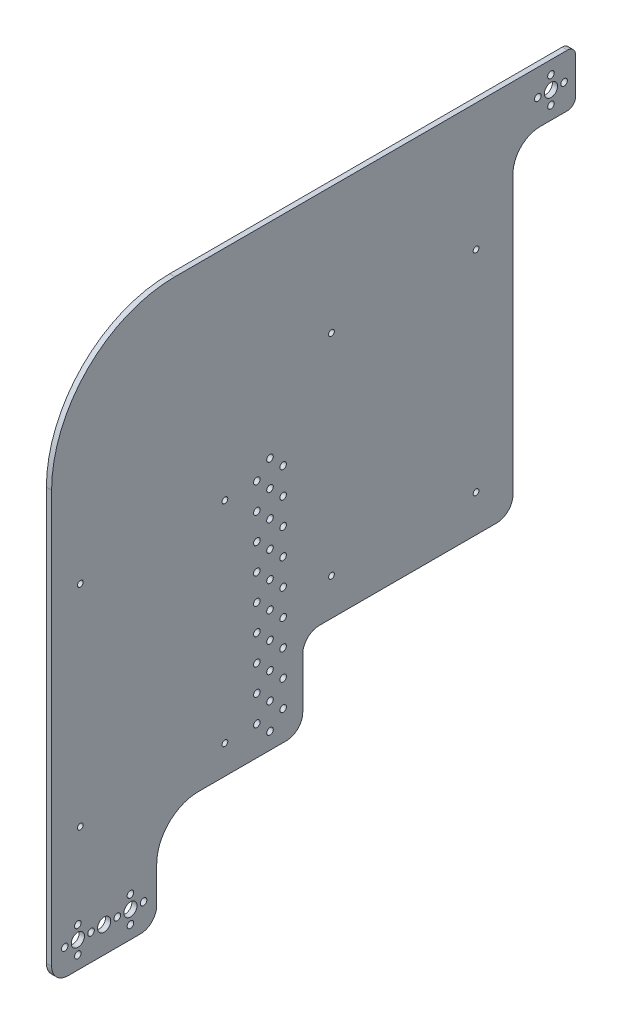
SolidWorks part; units mm, degrees
ref_plane "Front" through (0, 0, 0) normal (0, 0, 1) x (1, 0, 0)
ref_plane "Top" through (0, 0, 0) normal (0, 1, 0) x (1, 0, 0)
ref_plane "Right" through (0, 0, 0) normal (1, 0, 0) x (0, 0, -1)
sketch "Sketch1" plane through (0, 0, 0) normal (1, 0, 0) x (0, 0, -1)
  line L0 (-248, -304) -> (-264, -304) construction
  line L1 (-272, -300) -> (-272, -308) construction
  line L2 (-240, -288) -> (-240, -310)
  line L3 (-250, -320) -> (-294, -320)
  line L4 (-304, -310) -> (-304, -288)
  line L5 (-16, 16) -> (10, 16)
  line L6 (15, 11) -> (15, -11)
  line L7 (10, -16) -> (-6.55, -16)
  line L8 (-240, -288) -> (-6.55, -16) construction
  line L9 (-229, 16) -> (-16, 16)
  line L10 (-304, -288) -> (-304, -59)
  line L11 (-151.1, -252.6) -> (-151.1, -221.8)
  line L12 (-141.1, -211.8) -> (-33.1, -211.8)
  line L13 (-23.1, -201.8) -> (-23.1, -32.55)
  line L14 (-214.6, -262.6) -> (-161.1, -262.6)
  line L15 (-6.55, -16) -> (-23.1, -16) construction
  line L16 (-191, -252.6) -> (-151.1, -252.6) construction
  line L17 (-179.05, -244.6) -> (-179.05, -228.6) construction
  line L18 (-286.5, -117.1) -> (-286.5, -245.1) construction
  line L19 (-294, -109.6) -> (-191, -109.6) construction
  line L20 (-294, -109.6) -> (-294, -252.6) construction
  line L21 (-294, -252.6) -> (-191, -252.6) construction
  line L22 (-191, -109.6) -> (-191, -252.6) construction
  line L23 (-286.5, -245.1) -> (-198.5, -245.1) construction
  line L24 (-198.5, -117.1) -> (-198.5, -245.1) construction
  line L25 (-286.5, -117.1) -> (-198.5, -117.1) construction
  line L26 (-133.6, -61.3) -> (-133.6, -189.3) construction
  line L27 (-141.1, -53.8) -> (-38.1, -53.8) construction
  line L28 (-141.1, -53.8) -> (-141.1, -196.8) construction
  line L29 (-141.1, -196.8) -> (-38.1, -196.8) construction
  line L30 (-38.1, -53.8) -> (-38.1, -196.8) construction
  line L31 (-133.6, -189.3) -> (-45.6, -189.3) construction
  line L32 (-45.6, -61.3) -> (-45.6, -189.3) construction
  line L33 (-133.6, -61.3) -> (-45.6, -61.3) construction
  circle A0 centre (-256, -304) radius 4
  circle A1 centre (0, 0) radius 4
  circle A2 centre (8, 0) radius 2
  circle A3 centre (0, -8) radius 2
  circle A4 centre (-8, 0) radius 2
  circle A5 centre (0, 8) radius 2
  circle A6 centre (-248, -304) radius 2
  circle A7 centre (-256, -312) radius 2
  circle A8 centre (-264, -304) radius 2 [skipped]
  circle A9 centre (-256, -296) radius 2
  circle A10 centre (-264, -304) radius 2
  circle A11 centre (-272, -304) radius 4
  circle A12 centre (-288, -312) radius 2
  circle A13 centre (-280, -304) radius 2
  circle A14 centre (-288, -296) radius 2
  circle A15 centre (-288, -304) radius 4
  circle A16 centre (-296, -304) radius 2
  arc A17 (-240, -310) -> (-250, -320) centre (-250, -310) cw
  arc A18 (-294, -320) -> (-304, -310) centre (-294, -310) cw
  arc A19 (10, 16) -> (15, 11) centre (10, 11) cw
  arc A20 (15, -11) -> (10, -16) centre (10, -11) cw
  arc A21 (-304, -59) -> (-229, 16) centre (-229, -59) cw
  arc A22 (-240, -288) -> (-214.6, -262.6) centre (-214.6, -288) cw
  arc A23 (-6.55, -16) -> (-23.1, -32.55) centre (-6.55, -32.55) ccw
  arc A24 (-33.1, -211.8) -> (-23.1, -201.8) centre (-33.1, -201.8) ccw
  arc A25 (-151.1, -252.6) -> (-161.1, -262.6) centre (-161.1, -252.6) cw
  arc A26 (-151.1, -221.8) -> (-141.1, -211.8) centre (-141.1, -221.8) cw
  circle A27 centre (-171.05, -252.6) radius 2
  circle A28 centre (-179.05, -244.6) radius 2
  circle A29 centre (-171.05, -236.6) radius 2
  circle A30 centre (-163.05, -244.6) radius 2
  circle A31 centre (-179.05, -228.6) radius 2
  circle A32 centre (-171.05, -220.6) radius 2
  circle A33 centre (-163.05, -228.6) radius 2
  circle A34 centre (-179.05, -212.6) radius 2
  circle A35 centre (-171.05, -204.6) radius 2
  circle A36 centre (-163.05, -212.6) radius 2
  circle A37 centre (-179.05, -196.6) radius 2
  circle A38 centre (-171.05, -188.6) radius 2
  circle A39 centre (-163.05, -196.6) radius 2
  circle A40 centre (-179.05, -180.6) radius 2
  circle A41 centre (-171.05, -172.6) radius 2
  circle A42 centre (-163.05, -180.6) radius 2
  circle A43 centre (-179.05, -164.6) radius 2
  circle A44 centre (-171.05, -156.6) radius 2
  circle A45 centre (-163.05, -164.6) radius 2
  circle A46 centre (-179.05, -148.6) radius 2
  circle A47 centre (-171.05, -140.6) radius 2
  circle A48 centre (-163.05, -148.6) radius 2
  circle A49 centre (-179.05, -132.6) radius 2
  circle A50 centre (-171.05, -124.6) radius 2
  circle A51 centre (-163.05, -132.6) radius 2
  circle A52 centre (-179.05, -116.6) radius 2
  circle A53 centre (-171.05, -108.6) radius 2
  circle A54 centre (-163.05, -116.6) radius 2
  circle A55 centre (-286.5, -117.1) radius 1.75
  circle A56 centre (-198.5, -117.1) radius 1.75
  circle A57 centre (-198.5, -245.1) radius 1.75
  circle A58 centre (-286.5, -245.1) radius 1.75
  circle A59 centre (-133.6, -61.3) radius 1.75
  circle A60 centre (-45.6, -61.3) radius 1.75
  circle A61 centre (-45.6, -189.3) radius 1.75
  circle A62 centre (-133.6, -189.3) radius 1.75
  point P18 (0, 0)
  point P27 (-256, -304)
  point P47 (-272, -320)
  point P58 (15, 0)
  point P75 (-151.1, -262.6)
  point P78 (-151.1, -211.8)
  point P81 (0, 0)
  point P91 (-171.05, -244.6)
  dimension "D1" = 8
  dimension "D4" = 4
  dimension "D14" = 10
  dimension "D15" = 5
  dimension "D19" = 75
  dimension "D24" = 10
  dimension "D27" = 3.5
  dimension "D40" = 3.5
  dimension "D2" = 256
  dimension "D3" = 304
  dimension "D5" = 8
  dimension "D7" = 8
  dimension "D10" = 16
  dimension "D11" = 16
  dimension "D12" = 16
  dimension "D13" = 16
  dimension "D16" = 15
  dimension "D17" = 16
  dimension "D18" = 16
  dimension "D20" = 88.9
  dimension "D21" = 25.4
  dimension "D22" = 50.8
  dimension "D23" = 38.1
  dimension "D25" = 10
  dimension "D26" = 10
  dimension "D28" = 143
  dimension "D29" = 4
  dimension "D30" = 8
  dimension "D32" = 16
  dimension "D33" = 103
  dimension "D34" = 7.5
  dimension "D35" = 7.5
  dimension "D36" = 7.5
  dimension "D37" = 7.5
  dimension "D38" = 15
  dimension "D39" = 15
  dimension "D41" = 143
  dimension "D42" = 103
  dimension "D43" = 7.5
  dimension "D44" = 7.5
  dimension "D45" = 7.5
  dimension "D46" = 7.5
  dimension "D9" = 2
  dimension "D31" = 9
  dimension "D6" = 4
  dimension "D8" = 4
extrude "Boss-Extrude1" add sketch "Sketch1" against normal blind 3.175
sketch "Sketch2" plane through (0, 0, 0) normal (1, 0, 0) x (0, 0, -1)
  line L0 (-252.45, -60.2) -> (-74.65, -60.2) construction
  line L1 (-304, -60.2) -> (-252.45, -60.2) construction
  line L2 (-304, -59) -> (-304, -310) construction
  line L3 (-74.65, -60.2) -> (-23.1, -60.2) construction
  line L4 (-23.1, -201.8) -> (-23.1, -32.55) construction
  line L5 (10, 16) -> (-229, 16) construction
  text T0 "8699" font "Century Gothic" height 63.5
  point P11 (0, 0)
  dimension "D1" = 177.8
  dimension "D2" = 76.2
